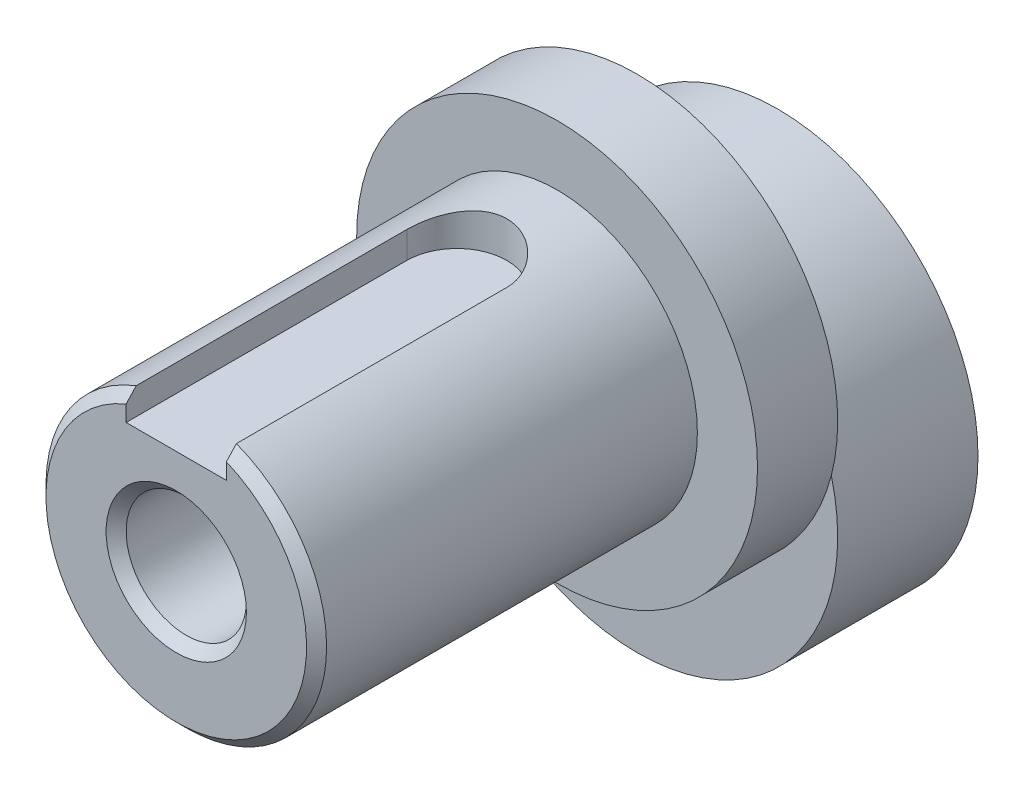
SolidWorks part; units mm, degrees
ref_plane "Front Plane" through (0, 0, 0) normal (0, 0, 1) x (1, 0, 0)
ref_plane "Top Plane" through (0, 0, 0) normal (0, 1, 0) x (1, 0, 0)
ref_plane "Right Plane" through (0, 0, 0) normal (1, 0, 0) x (0, 0, -1)
sketch "Sketch2" plane through (0, 0, 0) normal (0, 0, 1) x (1, 0, 0)
  circle A0 centre (0, 0) radius 10
  dimension "D1" = 20
extrude "Boss-Extrude1" add sketch "Sketch2" along normal blind 7
sketch "Sketch3" plane through (0, 0, 7) normal (0, 0, 1) x (1, 0, 0)
  line L0 (0, 0) -> (0, 5) construction
  circle A0 centre (0, 5) radius 10
  dimension "D2" = 20
  dimension "D1" = 5
extrude "Boss-Extrude2" add sketch "Sketch3" along normal blind 4 contours A0
sketch "Sketch4" plane through (0, 0, 11) normal (0, 0, 1) x (1, 0, 0)
  circle A0 centre (0, 5) radius 7
  dimension "D1" = 14
extrude "Boss-Extrude3" add sketch "Sketch4" along normal blind 19
sketch "Sketch5" plane through (0, 0, 30) normal (0, 0, 1) x (1, 0, 0)
  circle A0 centre (0, 5) radius 3
  point P3 (0, 0)
  dimension "D1" = 6
extrude "Cut-Extrude1" cut sketch "Sketch5" against normal through all
chamfer "Chamfer1" distance 0.5 angle 45 2 edges at (3, 5, 0) (3, 5, 30)
sketch "Sketch6" plane through (0, 0, 0) normal (0, 1, 0) x (1, 0, 0)
  line L0 (0, -11) -> (0, -30) construction
  line L1 (-7, -11) -> (7, -11) construction
  line L2 (-7, -30) -> (7, -30) construction
  line L5 (-2.5, -16) -> (-2.5, -31.7303)
  line L6 (-2.5, -31.7303) -> (2.5, -31.7303)
  line L7 (2.5, -16) -> (2.5, -31.7303)
  arc A0 (2.5, -16) -> (-2.5, -16) centre (0, -16) ccw
  dimension "D4" = 2.5
  dimension "D1" = 90
  dimension "D2" = 5
  dimension "D3" = 14
extrude "Cut-Extrude3" cut sketch "Sketch6" along normal through all from offset 10.2 contours L5 L6 L7 A0
chamfer "Chamfer2" distance 0.5 angle 45 1 edges at (0, -2, 30)
